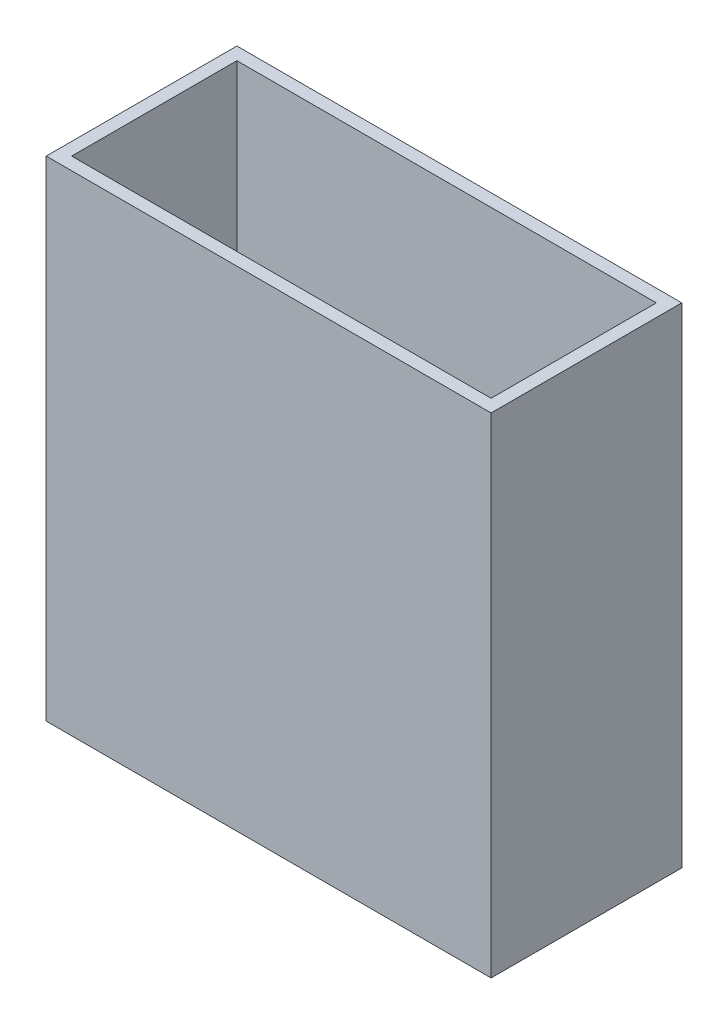
SolidWorks part; units mm, degrees
ref_plane "Front Plane" through (0, 0, 0) normal (0, 0, 1) x (1, 0, 0)
ref_plane "Top Plane" through (0, 0, 0) normal (0, 1, 0) x (1, 0, 0)
ref_plane "Right Plane" through (0, 0, 0) normal (1, 0, 0) x (0, 0, -1)
sketch "Sketch1" plane through (0, 0, 0) normal (0, 1, 0) x (1, 0, 0)
  line L1 (0, 0) -> (140, 0)
  line L2 (0, 0) -> (0, -60)
  line L3 (0, -60) -> (140, -60)
  line L4 (140, 0) -> (140, -60)
  line L5 (4, -4) -> (136, -4)
  line L6 (4, -4) -> (4, -56)
  line L7 (4, -56) -> (136, -56)
  line L8 (136, -4) -> (136, -56)
  dimension "D1" = 60
  dimension "D2" = 140
  dimension "D3" = 4
  dimension "D4" = 4
  dimension "D5" = 4
  dimension "D6" = 4
extrude "Boss-Extrude1" add sketch "Sketch1" along normal blind 150
sketch "Sketch2" plane through (0, 0, 0) normal (0, 1, 0) x (1, 0, 0)
  line L1 (0, 0) -> (140, 0)
  line L2 (0, 0) -> (0, -60)
  line L3 (0, -60) -> (140, -60)
  line L4 (140, 0) -> (140, -60)
sketch "Sketch3" plane through (0, 0, 0) normal (0, 0, 1) x (1, 0, 0)
  line L0 (0, 0) -> (140, 6)
  line L1 (140, 150) -> (140, 0) construction
  line L2 (140, 6) -> (140, -4)
  line L3 (140, -4) -> (0, -4)
  line L4 (0, -4) -> (0, 0)
  dimension "D1" = 4
  dimension "D2" = 10
extrude "Boss-Extrude3" add sketch "Sketch3" along normal up to surface (60 mm away) up to face at (70, 75, 60)
sketch "Sketch4" plane through (0, 0, 0) normal (-1, 0, 0) x (0, 0, 1)
  line L0 (30, 0) -> (30, 2) construction
  line L1 (0, 0) -> (60, 0) construction
  line L2 (30, 4.5) -> (30, 2) construction
  line L3 (27, 0) -> (33, 0)
  line L4 (27, 0) -> (27, 2)
  line L6 (33, 0) -> (33, 2)
  ellipse E0 centre (30, 2) end of major axis (27, 2) minor radius 2.5 (27, 2) -> (33, 2) cw
  dimension "D1" = 6
  dimension "D2" = 2
  dimension "D3" = 2.5
extrude "Cut-Extrude1" cut sketch "Sketch4" against normal up to surface (4 mm away) up to face at (4, 75.0857, 30)
sketch "Sketch5" plane through (0, 0, 0) normal (-1, 0, 0) x (0, 0, 1)
  line L0 (30, 0) -> (30, 12.9505) construction
  line L1 (0, 0) -> (60, 0) construction
  line L2 (60, -4) -> (0, -4) construction
  line L3 (19, 7) -> (41, 7) construction
  line L4 (38.5, 9.05) -> (38.5, 4.95)
  line L5 (19, 9.05) -> (21.5, 9.05)
  line L6 (19, 9.05) -> (19, 4.95)
  line L7 (19, 4.95) -> (21.5, 4.95)
  line L8 (21.5, 9.05) -> (21.5, 4.95)
  line L9 (41, 4.95) -> (38.5, 4.95)
  line L10 (41, 9.05) -> (41, 4.95)
  line L11 (41, 9.05) -> (38.5, 9.05)
  circle A0 centre (30, 7) radius 11 construction
  point P14 (0, 0)
  dimension "D1" = 22
  dimension "D2" = 4.1
  dimension "D3" = 2.5
extrude "Cut-Extrude2" cut sketch "Sketch5" against normal blind 4
